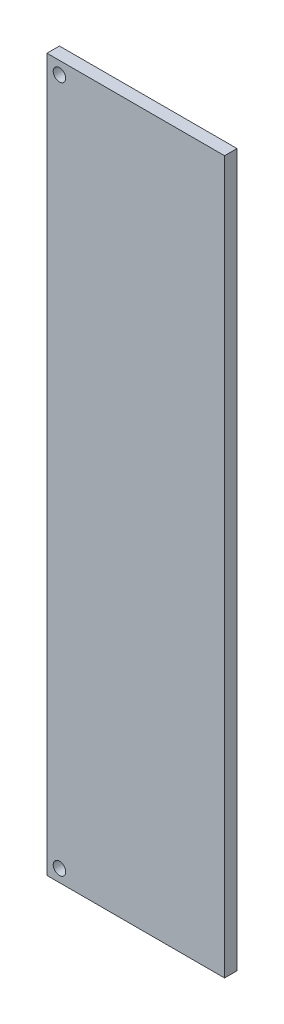
SolidWorks part; units mm, degrees
ref_plane "Front Plane" through (0, 0, 0) normal (0, 0, 1) x (1, 0, 0)
ref_plane "Top Plane" through (0, 0, 0) normal (0, 1, 0) x (1, 0, 0)
ref_plane "Right Plane" through (0, 0, 0) normal (1, 0, 0) x (0, 0, -1)
sketch "Sketch1" plane through (0, 0, 0) normal (0, 0, 1) x (1, 0, 0)
  line L1 (-92.3735, 63.8735) -> (-63.8735, 63.8735)
  line L2 (-92.3735, 63.8735) -> (-92.3735, -50.4265)
  line L3 (-92.3735, -50.4265) -> (-63.8735, -50.4265)
  line L4 (-63.8735, 63.8735) -> (-63.8735, -50.4265)
  dimension "D1" = 114.3
  dimension "D2" = 28.5
extrude "Boss-Extrude1" add sketch "Sketch1" along normal blind 2
sketch "Sketch2" plane through (0, 0, 2) normal (0, 0, 1) x (1, 0, 0)
  line L0 (-92.3735, -50.4265) -> (-63.8735, -50.4265) construction
  line L1 (-92.3735, 63.8735) -> (-92.3735, -50.4265) construction
  line L2 (-63.8735, 63.8735) -> (-92.3735, 63.8735) construction
  circle A0 centre (-90.3735, 61.8735) radius 1
  circle A1 centre (-90.3735, -48.4265) radius 1
  dimension "D1" = 2
  dimension "D3" = 2
  dimension "D4" = 2
  dimension "D6" = 2
  dimension "D2" = 2
  dimension "D5" = 2
extrude "Cut-Extrude1" cut sketch "Sketch2" against normal through all
